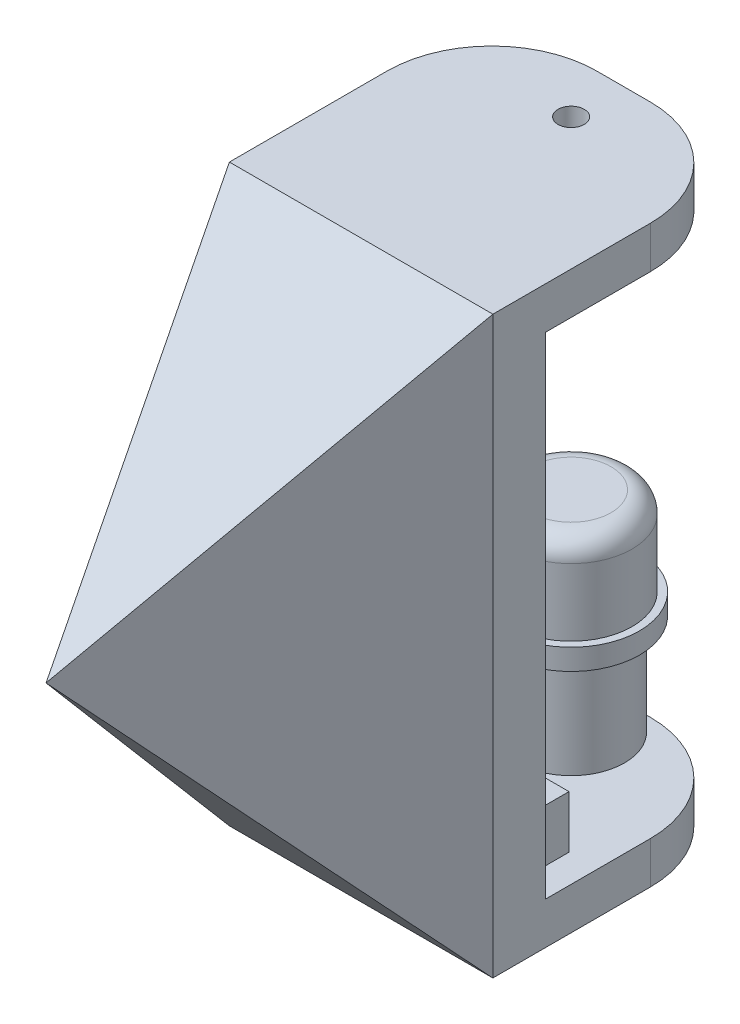
SolidWorks part; units mm, degrees
ref_plane "Front Plane" through (0, 0, 0) normal (0, 0, 1) x (1, 0, 0)
ref_plane "Top Plane" through (0, 0, 0) normal (0, 1, 0) x (1, 0, 0)
ref_plane "Right Plane" through (0, 0, 0) normal (1, 0, 0) x (0, 0, -1)
sketch "Sketch4" plane through (0, 0, 0) normal (0, 0, 1) x (1, 0, 0)
  line L1 (-6.23, -9.975) -> (6.23, -9.975)
  line L2 (-6.23, -9.975) -> (-6.23, 7.275)
  line L3 (-6.23, 7.275) -> (6.23, 7.275)
  line L4 (6.23, -9.975) -> (6.23, 7.275)
  point P4 (0, 7.275)
  dimension "D1" = 12.46
  dimension "D2" = 17.25
  dimension "D3" = 9.975
extrude "Boss-Extrude3" add sketch "Sketch4" along normal blind 6
sketch "Sketch8" plane through (0, -9.975, 0) normal (0, -1, 0) x (-1, 0, 0)
  circle A0 centre (0, -23.55) radius 12.5468
  circle A1 centre (0, -23.55) radius 11.15
  dimension "D1" = 22.3
  dimension "D2" = 23.55
extrude "Boss-Extrude6" add sketch "Sketch8" along normal blind 7.3 and the other way up to surface (17.25 mm away) other way up to face at (0, 7.275, 3)
sketch "Sketch5" plane through (0, 7.275, 0) normal (0, 1, 0) x (1, 0, 0)
  line L8 (12.5468, -23.55) -> (12.5468, 0)
  line L9 (12.5468, 0) -> (6.23, 0)
  line L10 (-12.5468, -23.55) -> (-12.5468, 0)
  line L11 (-12.5468, 0) -> (-6.23, 0)
  line L12 (-6.23, 0) -> (-6.23, -29.7)
  line L14 (6.23, -29.7) -> (6.23, 0)
  line L15 (-6.23, -29.7) -> (6.23, -29.7)
  line L16 (6.23, -6) -> (-6.23, -6) construction
  circle A0 centre (0, -23.55) radius 12.5468 construction
  arc A1 (-12.5468, -23.55) -> (12.5468, -23.55) centre (0, -23.55) ccw
  dimension "D1" = 23.7
  dimension "D2" = 23.55
extrude "Boss-Extrude4" add sketch "Sketch5" against normal up to surface (17.25 mm away) up to face at (0, -9.975, 3)
sketch "Sketch6" plane through (0, 7.275, 0) normal (0, 1, 0) x (1, 0, 0)
  line L0 (6.23, -6) -> (-6.23, -6) construction
  line L3 (6.23, -29.7) -> (-6.23, -29.7) construction
  circle A0 centre (0, -3.6) radius 0.5
  circle A1 centre (0, -32.1) radius 0.5
  dimension "D1" = 1
  dimension "D3" = 1
  dimension "D2" = 2.4
  dimension "D4" = 2.4
extrude "Cut-Extrude1" cut sketch "Sketch6" against normal blind 15
chamfer "Chamfer1" distance 0.5 angle 60 2 edges at (0, 7.275, 4.1) (0, 7.275, 32.6)
sketch "Sketch10" plane through (0, 7.275, 0) normal (0, 1, 0) x (1, 0, 0)
  line L1 (-6.23, -6) -> (6.23, -6)
  line L2 (-6.23, -6) -> (-6.23, -29.7)
  line L3 (-6.23, -29.7) -> (6.23, -29.7)
  line L4 (6.23, -6) -> (6.23, -29.7)
extrude "Cut-Extrude3" cut sketch "Sketch10" against normal up to surface (17.25 mm away) up to face at (0, -9.975, 10.3399)
ref_plane "Plane1" through (0, 0, 36.0968) normal (0, 0, 1) x (1, 0, 0)
sketch "Sketch11" plane through (0, 0, 36.0968) normal (0, 0, 1) x (1, 0, 0)
  line L0 (-11.15, -9.975) -> (11.15, -9.975) construction
  line L1 (-2.5, -6.975) -> (2.5, -6.975)
  line L2 (-2.5, -6.975) -> (-2.5, -9.975)
  line L3 (-2.5, -9.975) -> (2.5, -9.975)
  line L4 (2.5, -6.975) -> (2.5, -9.975)
  point P4 (0, -6.975)
  dimension "D1" = 0
  dimension "D2" = 5
  dimension "D3" = 3
extrude "Cut-Extrude4" cut sketch "Sketch11" against normal up to next
sketch "Sketch13" plane through (0, -17.275, 0) normal (0, -1, 0) x (1, 0, 0)
  line L0 (-12.5468, 23.55) -> (-12.5468, 0)
  line L1 (-12.5468, 0) -> (12.5468, 0)
  line L2 (12.5468, 0) -> (12.5468, 23.55)
  arc A0 (-12.5468, 23.55) -> (12.5468, 23.55) centre (0, 23.55) ccw
  point P3 (0, 0)
extrude "Boss-Extrude7" add sketch "Sketch13" against normal up to surface (7.3 mm away) up to face at (0, -9.975, 10.3399)
sketch "Sketch15" plane through (0, 7.275, 0) normal (0, 1, 0) x (1, 0, 0)
  line L0 (-12.5468, 0) -> (12.5468, 0)
  line L1 (12.5468, 0) -> (12.5468, -23.55)
  line L2 (-12.5468, 0) -> (-12.5468, -23.55)
  line L3 (6.23, -6) -> (6.23, -29.7) construction
  line L4 (-6.23, -0.8) -> (6.23, -0.8)
  line L5 (-6.23, -0.8) -> (-6.23, -33.5)
  line L6 (-5.23, -34.5) -> (5.23, -34.5)
  line L7 (6.23, -0.8) -> (6.23, -33.5)
  arc A0 (-12.5468, -23.55) -> (12.5468, -23.55) centre (0, -23.55) ccw
  circle A1 centre (0, -3.6) radius 0.5 construction
  arc A2 (5.23, -34.5) -> (6.23, -33.5) centre (5.23, -33.5) ccw
  arc A3 (-6.23, -33.5) -> (-5.23, -34.5) centre (-5.23, -33.5) ccw
  point P15 (0, -0.8)
  dimension "D1" = 0.8
  dimension "D3" = 1
  dimension "D2" = 2.8
  dimension "D4" = 0
  dimension "D5" = 34.5
extrude "Boss-Extrude9" add sketch "Sketch15" along normal blind 10
sketch "Sketch20" plane through (0, -17.275, 0) normal (0, -1, 0) x (1, 0, 0)
  circle A0 centre (0, 23.55) radius 7.15
  circle A1 centre (0, 23.55) radius 11.15
  circle A2 centre (0, 23.55) radius 11.15 construction
  dimension "D1" = 14.3
extrude "Boss-Extrude11" add sketch "Sketch20" against normal up to surface (7.3 mm away) up to face at (-6.0145, -9.975, 27.3356)
sketch "Sketch21" plane through (0, -17.275, 0) normal (0, -1, 0) x (1, 0, 0)
  circle A0 centre (0, 23.55) radius 7.15
  circle A1 centre (0, 23.55) radius 10.15
  circle A2 centre (0, 23.55) radius 7.15 construction
  dimension "D1" = 20.3
extrude "Cut-Extrude7" cut sketch "Sketch21" against normal blind 1.3
sketch "Sketch17" plane through (12.5468, 4.7282, 0) normal (-1, 0, 0) x (0, 1, 0)
  line L0 (16.9468, 25) -> (16.9468, 0)
  line L1 (16.9468, 0) -> (-37.8032, 0)
  line L2 (-37.8032, 0) -> (-37.8032, 25)
  line L3 (-37.8032, 25) -> (-33.8032, 25)
  line L4 (-33.8032, 25) -> (-33.8032, 5)
  line L5 (-33.8032, 5) -> (12.9468, 5)
  line L6 (12.9468, 5) -> (12.9468, 25)
  line L7 (12.9468, 25) -> (16.9468, 25)
  line L8 (-22.0032, -23.55) -> (-22.0032, 0) construction
  line L10 (12.5468, 0) -> (12.5468, -23.55) construction
  dimension "D1" = 4
  dimension "D2" = 0.4
  dimension "D3" = 4
  dimension "D4" = 25
  dimension "D5" = 5
  dimension "D6" = 15.8
extrude "Boss-Extrude10" add sketch "Sketch17" along normal up to surface (25.0936 mm away) up to face at (-12.5468, 0, 11.775)
sketch "Sketch18" plane through (0, 17.675, 0) normal (0, -1, 0) x (0, 0, 1)
  line L0 (-25, -12.5468) -> (-25, 12.5468) construction
  line L1 (-25, 6.2191) -> (-5, 6.2191)
  line L2 (-25, 6.2191) -> (-25, -6.2191)
  line L3 (-25, -6.2191) -> (-5, -6.2191)
  line L4 (-5, 6.2191) -> (-5, -6.2191)
  line L5 (-5, -12.5468) -> (-5, 12.5468) construction
  point P6 (-25, 0)
  point P7 (-25, 0)
  dimension "D1" = 0
extrude "Cut-Extrude5" cut sketch "Sketch18" against normal blind 2
sketch "Sketch19" plane through (0, 19.675, 0) normal (0, -1, 0) x (0, 0, 1)
  line L0 (-25, -12.5468) -> (-25, 12.5468) construction
  circle A0 centre (-20, 0) radius 1.25
  dimension "D1" = 2.5
  dimension "D2" = 5
extrude "Cut-Extrude6" cut sketch "Sketch19" against normal through all both and the other way through all
fillet "Fillet1" radius 10 4 edges at (-12.5468, 19.675, -25) (12.5468, 19.675, -25) (12.5468, -31.075, -25) (-12.5468, -31.075, -25)
ref_plane "Plane2" through (0, 0, 0) normal (1, 0, 0) x (0, 0, -1)
ref_plane "Plane3" through (0, 0, 0) normal (0, -1, 0) x (-1, 0, 0)
sketch "Sketch22" plane through (0, -29.075, 0) normal (0, 1, 0) x (0, 0, -1)
  circle A0 centre (20, 0) radius 5.8
  dimension "D1" = 11.6
extrude "Boss-Extrude12" add sketch "Sketch22" along normal blind 20
fillet "Fillet2" radius 2 1 edges at (-5.8, -9.075, -20)
sketch "Sketch23" plane through (0, -29.075, 0) normal (0, 1, 0) x (0, 0, -1)
  circle A0 centre (20, 0) radius 5.08
  circle A1 centre (20, 0) radius 5.9309
  dimension "D1" = 10.16
extrude "Cut-Extrude8" cut sketch "Sketch23" along normal blind 11.6
sketch "Sketch24" plane through (0, -17.475, 0) normal (0, -1, 0) x (0, 0, 1)
  circle A0 centre (-20, 0) radius 6.5
extrude "Boss-Extrude13" add sketch "Sketch24" along normal blind 2
sketch "Sketch25" plane through (0, -33.075, 0) normal (0, -1, 0) x (0, 0, 1)
  circle A0 centre (-20, 0) radius 1.25
extrude "Boss-Extrude14" add sketch "Sketch25" against normal blind 2
sketch "Sketch26" plane through (0, -29.075, 0) normal (0, 1, 0) x (0, 0, -1)
  line L0 (5, -12.5468) -> (5, 12.5468) construction
  line L1 (5, -9.7968) -> (10, -9.7968)
  line L2 (5, -9.7968) -> (5, -6.7968)
  line L3 (5, -6.7968) -> (10, -6.7968)
  line L4 (10, -9.7968) -> (10, -6.7968)
  line L6 (5, -5.2808) -> (10, -5.2808)
  line L7 (5, -5.2808) -> (5, -2.2808)
  line L8 (5, -2.2808) -> (10, -2.2808)
  line L9 (10, -5.2808) -> (10, -2.2808)
  line L10 (5, -12.5468) -> (15, -12.5468) construction
  dimension "D1" = 1.516
  dimension "D2" = 3
  dimension "D3" = 3
  dimension "D4" = 0
  dimension "D5" = 5
  dimension "D6" = 2.75
extrude "Boss-Extrude15" add sketch "Sketch26" along normal blind 5
sketch "Sketch27" plane through (0, 17.275, 0) normal (0, 1, 0) x (1, 0, 0)
  line L1 (-12.5468, 0) -> (14.6865, 0)
  line L2 (-12.5468, 0) -> (-12.5468, -38.6054)
  line L3 (-12.5468, -38.6054) -> (14.6865, -38.6054)
  line L4 (14.6865, 0) -> (14.6865, -38.6054)
extrude "Cut-Extrude9" cut sketch "Sketch27" against normal through all
sketch "Sketch28" plane through (0, 21.675, 0) normal (0, 1, 0) x (1, 0, 0)
  line L0 (12.5468, 0) -> (0, -30)
  line L1 (0, -30) -> (-12.5468, 0)
  line L2 (-12.5468, 0) -> (12.5468, 0)
  dimension "D1" = 30
  dimension "D2" = 0
extrude "Boss-Extrude16" add sketch "Sketch28" against normal up to surface (54.75 mm away) up to face at (0, -33.075, -14.0237)
sketch "Sketch29" plane through (0, 0, 0) normal (1, 0, 0) x (0, 0, -1)
  line L0 (0, 21.675) -> (-30, 21.675)
  line L1 (-30, 21.675) -> (-30, 0)
  line L2 (-30, -33.075) -> (-30, 21.675) construction
  line L3 (-30, 0) -> (0, 21.675)
  line L4 (0, -33.075) -> (-30, -33.075)
  line L5 (-30, -33.075) -> (-30, -0.02)
  line L6 (-30, -0.02) -> (0, -33.075)
  point P13 (-30, -5.7)
  dimension "D1" = 5.7
  dimension "D2" = 0.02
extrude "Cut-Extrude10" cut sketch "Sketch29" against normal through all both and the other way through all
sketch "Sketch30" plane through (0, 0, -5) normal (0, 0, -1) x (-1, 0, 0)
  line L0 (12.5468, 21.675) -> (0, 0)
  line L1 (0, 8.25) -> (0, -8.25) construction
  line L2 (0, 0) -> (12.5468, -29.075)
  line L3 (12.5468, -29.075) -> (12.5468, 21.675)
  point P5 (0, 0)
extrude "Cut-Extrude11" cut sketch "Sketch30" against normal through all
